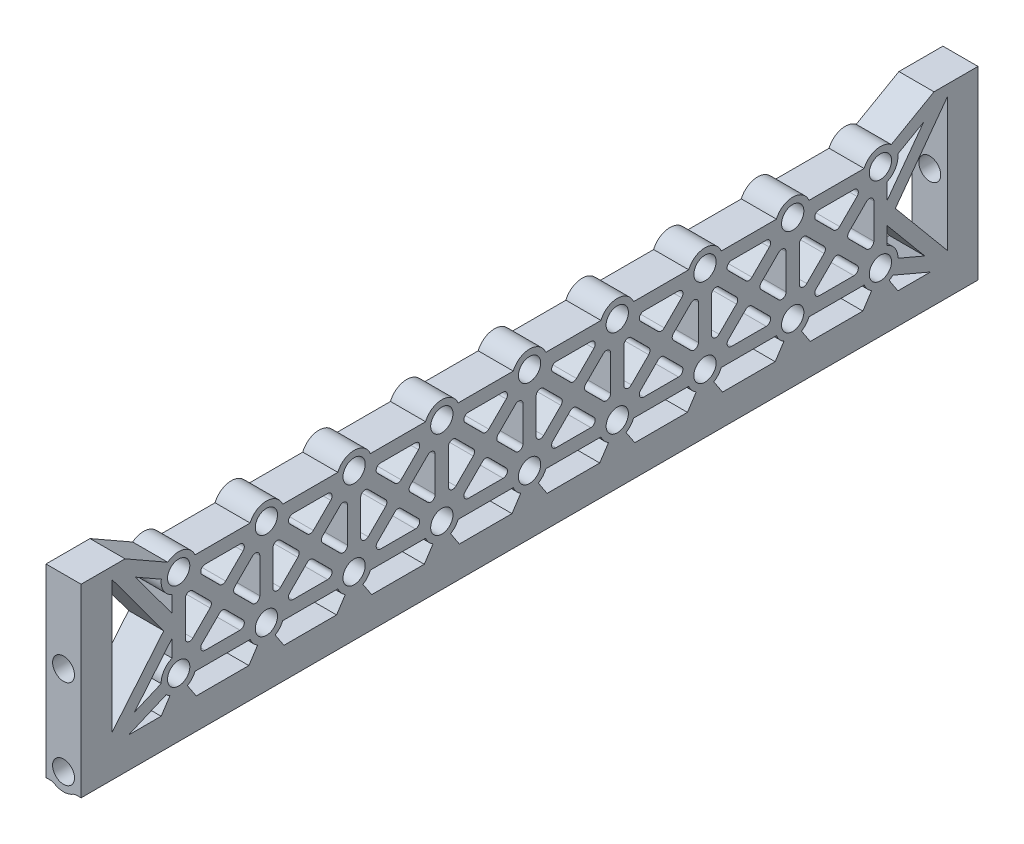
SolidWorks part; units mm, degrees
ref_plane "Front Plane" through (0, 0, 0) normal (0, 0, 1) x (1, 0, 0)
ref_plane "Top Plane" through (0, 0, 0) normal (0, 1, 0) x (1, 0, 0)
ref_plane "Right Plane" through (0, 0, 0) normal (1, 0, 0) x (0, 0, -1)
sketch "Sketch1" plane through (218.75, 0, 0) normal (1, 0, 0) x (0, 0, -1)
  line L0 (-102.25, 41.675) -> (-102.25, 55.65) construction
  line L1 (-102.25, 37.185) -> (102.25, 37.185)
  line L2 (-102.25, 37.185) -> (-102.25, -5)
  line L3 (-102.25, -5) -> (102.25, -5)
  line L4 (102.25, 37.185) -> (102.25, -5)
  line L6 (102.25, -5) -> (-102.25, -5) construction
  line L7 (102.25, 51.04) -> (102.25, 45.96) construction
extrude "Boss-Extrude1" add sketch "Sketch1" against normal blind 8
hole_wizard "Ø5.0mm Dowel Hole1" positions "Sketch4" profile "Sketch3" hole size "Ø5.0" standard "ANSI Metric"
sketch "Sketch4" plane through (0, 0, -102.25) normal (0, 0, -1) x (-1, 0, 0)
  point P0 (-214.75, 18.5)
  point P3 (-214.75, -1.825)
sketch "Sketch3" plane through (214.75, 18.5, -102.25) normal (1, 0, 0) x (0, 1, 0)
  line L0 (0, 0) -> (0, 11.5022)
  line L1 (0, 11.5022) -> (2.5, 10)
  line L2 (2.5, 10) -> (2.5, 0)
  line L5 (2.5, 0) -> (0, 0)
  line L10 (0, 11.5022) -> (-2.5, 10) construction
  line L11 (0, -6.35) -> (0, 107.95) construction
  dimension "Hole Dia." = 5
  dimension "Hole Depth" = 10
  dimension "Drill Angle" = 118
sketch "Sketch5" plane through (0, 0, -102.25) normal (0, 0, -1) x (-1, 0, 0)
  line L0 (-218.75, -5) -> (-218.75, 37.185) construction
  circle A0 centre (-214.75, -1.825) radius 4
  circle A1 centre (-214.75, -1.825) radius 2.5 construction
  circle A2 centre (-214.75, -1.825) radius 2.5
extrude "Boss-Extrude2" add sketch "Sketch5" against normal blind 10
fillet "Fillet1" radius 2 2 edges at (212.317, -5, -97.25) (217.183, -5, -97.25)
mirror "Mirror2" about plane through (0, 0, 0) normal (0, 0, 1) of "Fillet1", "Boss-Extrude2", "Ø5.0mm Dowel Hole1"
sketch "Sketch6" plane through (218.75, 0, 0) normal (1, 0, 0) x (0, 0, -1)
  line L0 (0, 28.5) -> (20, 28.5) construction
  line L1 (0, 28.5) -> (0, 8.5) construction
  line L2 (-95.25, 37.185) -> (-102.25, 37.185)
  line L3 (-102.25, 37.185) -> (-102.25, -5)
  line L4 (-102.25, -5) -> (102.25, -5)
  line L5 (102.25, -5) -> (102.25, 37.185)
  line L6 (102.25, 37.185) -> (95.25, 37.185)
  line L7 (-95.25, 37.185) -> (95.25, 37.185)
  line L10 (0, 0) -> (0, 28.5) construction
  line L11 (-95.25, 30.185) -> (-95.25, 37.185)
  line L12 (102.25, 37.185) -> (-102.25, 37.185) construction
  line L13 (95.25, 30.185) -> (95.25, 37.185)
  line L14 (95.25, 2) -> (95.25, 30.185)
  line L15 (-95.25, 2) -> (95.25, 2)
  line L16 (-95.25, 30.185) -> (-95.25, 2)
  line L17 (95.25, 30.185) -> (-95.25, 30.185)
  line L18 (95.25, 2) -> (95.25, 30.185)
  line L19 (-95.25, 2) -> (95.25, 2)
  line L20 (-95.25, 30.185) -> (-95.25, 2)
  circle A0 centre (0, 28.5) radius 2.54
  circle A1 centre (0, 28.5) radius 4
  circle A2 centre (20, 28.5) radius 4
  circle A3 centre (20, 28.5) radius 2.54
  circle A4 centre (40, 28.5) radius 4
  circle A5 centre (40, 28.5) radius 2.54
  circle A6 centre (60, 28.5) radius 4
  circle A7 centre (60, 28.5) radius 2.54
  circle A8 centre (80, 28.5) radius 4
  circle A9 centre (80, 28.5) radius 2.54
  circle A10 centre (20, 8.5) radius 4
  circle A11 centre (20, 8.5) radius 2.54
  circle A12 centre (40, 8.5) radius 4
  circle A13 centre (40, 8.5) radius 2.54
  circle A14 centre (60, 8.5) radius 4
  circle A15 centre (60, 8.5) radius 2.54
  circle A16 centre (80, 8.5) radius 4
  circle A17 centre (80, 8.5) radius 2.54
  circle A18 centre (0, 8.5) radius 4
  circle A19 centre (0, 8.5) radius 2.54
  circle A20 centre (-80, 8.5) radius 2.54
  circle A21 centre (-80, 8.5) radius 4
  circle A22 centre (-60, 8.5) radius 2.54
  circle A23 centre (-60, 8.5) radius 4
  circle A24 centre (-40, 8.5) radius 2.54
  circle A25 centre (-40, 8.5) radius 4
  circle A26 centre (-20, 8.5) radius 2.54
  circle A27 centre (-20, 8.5) radius 4
  circle A28 centre (-80, 28.5) radius 2.54
  circle A29 centre (-80, 28.5) radius 4
  circle A30 centre (-60, 28.5) radius 2.54
  circle A31 centre (-60, 28.5) radius 4
  circle A32 centre (-40, 28.5) radius 2.54
  circle A33 centre (-40, 28.5) radius 4
  circle A34 centre (-20, 28.5) radius 2.54
  circle A35 centre (-20, 28.5) radius 4
  line M6 (102.25, 37.185) -> (-102.25, 37.185)
  dimension "D3" = 5.08
  dimension "D4" = 8
  dimension "D2" = 28.5
  dimension "D7" = 20
  dimension "D8" = 20
  dimension "D1" = 7
  dimension "D5" = 5
  dimension "D6" = 2
extrude "Cut-Extrude1" cut sketch "Sketch6" against normal through all contours L11 L20 L19 L18 L13 A18 A16 A14 A12 A10 A8 A6 A4 A2 A1 A21 A23 A25 A27 A29 A31 A33 A35 M6 | A28 | A20 | A22 | A30 | A32 | A34 | A0 | A19 | A26 | A24 | A3 | A5 | A7 | A9 | A11 | A13 | A15 | A17
sketch "Sketch7" plane through (218.75, 0, 0) normal (1, 0, 0) x (0, 0, -1)
  line L0 (-80, 28.5) -> (-60, 28.5) construction
  line L1 (-60, 28.5) -> (-60, 8.5) construction
  line L2 (-60, 8.5) -> (-80, 8.5) construction
  line L3 (-80, 8.5) -> (-80, 28.5) construction
  line L4 (-80, 28.5) -> (-60, 8.5) construction
  line L5 (-80, 8.5) -> (-60, 28.5) construction
  line L6 (-74.6716, 25.2929) -> (-70.7071, 21.3284)
  line L7 (-76.2919, 30) -> (-63.7081, 30)
  line L8 (-58.5, 24.7919) -> (-58.5, 12.2081)
  line L9 (-78.9393, 29.5607) -> (-58.9393, 9.5607) construction
  line L10 (-73.9645, 27) -> (-66.0355, 27)
  line L11 (-63.7081, 7) -> (-76.2919, 7)
  line L12 (-69.2929, 21.3284) -> (-65.3284, 25.2929)
  line L13 (-81.5, 12.2081) -> (-81.5, 24.7919)
  line L14 (-58.5, 7) -> (-81.5, 7) construction
  line L15 (-58.5, 30) -> (-58.5, 7) construction
  line L16 (-81.5, 30) -> (-58.5, 30) construction
  line L17 (-81.5, 7) -> (-81.5, 30) construction
  line L18 (-61.5, 22.4645) -> (-61.5, 14.5355)
  line L19 (-67.1716, 17.7929) -> (-63.2071, 13.8284)
  line L20 (-63.2071, 23.1716) -> (-67.1716, 19.2071)
  line L21 (-66.0355, 10) -> (-73.9645, 10)
  line L22 (-70.7071, 15.6716) -> (-74.6716, 11.7071)
  line L23 (-65.3284, 11.7071) -> (-69.2929, 15.6716)
  line L24 (-78.5, 14.5355) -> (-78.5, 22.4645)
  line L25 (-72.8284, 19.2071) -> (-76.7929, 23.1716)
  line L26 (-76.7929, 13.8284) -> (-72.8284, 17.7929)
  line L27 (-70, 18.5) -> (-69.2929, 21.3284) construction
  arc A0 (-70.7071, 21.3284) -> (-69.2929, 21.3284) centre (-70, 22.0355) ccw
  arc A1 (-65.3284, 25.2929) -> (-66.0355, 27) centre (-66.0355, 26) ccw
  arc A2 (-73.9645, 27) -> (-74.6716, 25.2929) centre (-73.9645, 26) ccw
  circle A3 centre (-80, 8.5) radius 4 construction
  circle A4 centre (-60, 8.5) radius 4 construction
  circle A5 centre (-60, 28.5) radius 4 construction
  circle A6 centre (-80, 28.5) radius 4 construction
  arc A7 (-76.2919, 7) -> (-81.5, 12.2081) centre (-80, 8.5) ccw
  arc A8 (-58.5, 12.2081) -> (-63.7081, 7) centre (-60, 8.5) ccw
  arc A9 (-63.7081, 30) -> (-58.5, 24.7919) centre (-60, 28.5) ccw
  arc A10 (-81.5, 24.7919) -> (-76.2919, 30) centre (-80, 28.5) ccw
  arc A11 (-61.5, 22.4645) -> (-63.2071, 23.1716) centre (-62.5, 22.4645) ccw
  arc A12 (-63.2071, 13.8284) -> (-61.5, 14.5355) centre (-62.5, 14.5355) ccw
  arc A13 (-67.1716, 19.2071) -> (-67.1716, 17.7929) centre (-66.4645, 18.5) ccw
  arc A14 (-66.0355, 10) -> (-65.3284, 11.7071) centre (-66.0355, 11) ccw
  arc A15 (-74.6716, 11.7071) -> (-73.9645, 10) centre (-73.9645, 11) ccw
  arc A16 (-69.2929, 15.6716) -> (-70.7071, 15.6716) centre (-70, 14.9645) ccw
  arc A17 (-78.5, 14.5355) -> (-76.7929, 13.8284) centre (-77.5, 14.5355) ccw
  arc A18 (-76.7929, 23.1716) -> (-78.5, 22.4645) centre (-77.5, 22.4645) ccw
  arc A19 (-72.8284, 17.7929) -> (-72.8284, 19.2071) centre (-73.5355, 18.5) ccw
  point P2 (-70, 18.5)
  dimension "D4" = 1
  dimension "D2" = 1.5
  dimension "D3" = 1.5
  dimension "D7" = 2.9155
  dimension "D1" = 1.5
  dimension "D5" = 1.5
  dimension "D6" = 4
extrude "Boss-Extrude3" add sketch "Sketch7" against normal up to surface (8 mm away) up to face at (210.75, 28.5, 57.46)
pattern_linear "LPattern1" count 8 spacing 20 along (0, 0, -1) of "Boss-Extrude3"
sketch "Sketch8" plane through (218.75, 0, 0) normal (1, 0, 0) x (0, 0, -1)
  line L0 (-95.25, 37.185) -> (-80, 28.5) construction
  line L2 (-81.5, 24.7919) -> (-81.5, 12.2081) construction
  line L3 (-80, 8.5) -> (-95.25, 2) construction
  line L5 (-95.25, 37.185) -> (-81.5, 18.5) construction
  line L6 (-81.5, 18.5) -> (-95.25, 2) construction
  line L7 (-95.25, 34.6542) -> (-82.489, 17.3132)
  line L8 (-92.219, 37.185) -> (-82.4799, 31.6385)
  line L10 (-81.5, 16.1569) -> (-90.1146, 5.8194)
  line L11 (-83.9993, 8.4259) -> (-90.1146, 5.8194)
  line L12 (-89.8573, 32.3876) -> (-81.5, 21.0308)
  line L13 (-89.8573, 32.3876) -> (-83.9645, 29.0316)
  line L16 (-82.823, 5.6662) -> (-91.4244, 2)
  line L17 (-81.5, 24.7919) -> (-81.5, 12.2081)
  line L18 (-95.25, 37.185) -> (-95.25, 2)
  line L19 (-95.25, 2) -> (-91.4244, 2)
  line L20 (-95.25, 2) -> (95.25, 2) construction
  line L21 (-95.25, 37.185) -> (-92.219, 37.185)
  line L22 (-100.6427, 41.9824) -> (-79.2577, 29.8034) construction
  line L23 (-100.6427, 41.9824) -> (-82.7081, 17.611) construction
  line L24 (-82.6523, 19.4603) -> (-100.3854, -1.8194) construction
  line L25 (-79.4119, 7.1201) -> (-100.3854, -1.8194) construction
  line L26 (-89.8573, 32.3876) -> (-80.7423, 27.1966) construction
  line L27 (-80.5881, 9.8799) -> (-90.1146, 5.8194) construction
  line L28 (-80.3477, 17.5397) -> (-90.1146, 5.8194) construction
  line L29 (-89.8573, 32.3876) -> (-80.2919, 19.389) construction
  line L31 (-82.4157, 19.7443) -> (-95.25, 4.3431)
  arc A1 (-81.5, 12.2081) -> (-76.2919, 7) centre (-80, 8.5) ccw construction
  arc A2 (-76.2919, 30) -> (-81.5, 24.7919) centre (-80, 28.5) ccw construction
  arc A3 (-81.5, 12.2081) -> (-76.2919, 7) centre (-80, 8.5) ccw
  arc A4 (-76.2919, 30) -> (-81.5, 24.7919) centre (-80, 28.5) ccw
  dimension "D1" = 1.5
  dimension "D3" = 1.5
  dimension "D2" = 1.5
extrude "Boss-Extrude4" add sketch "Sketch8" against normal up to surface (8 mm away) up to face at (210.75, 17.8425, 0)
mirror "Mirror3" about plane through (0, 0, 0) normal (0, 0, 1) of "Boss-Extrude4"
sketch "Sketch9" plane through (218.75, 0, 0) normal (1, 0, 0) x (0, 0, -1)
  line L0 (-82, 5.0359) -> (-78, 5.0359) construction
  line L1 (-78, 5.0359) -> (-76, 2)
  line L2 (-91.4244, 2) -> (91.4244, 2) construction
  line L3 (-76, 2) -> (-84, 2)
  line L4 (-84, 2) -> (-82, 5.0359)
  line L5 (-82, 5.0359) -> (-78, 5.0359)
  arc A0 (-82.823, 5.6662) -> (-76.2919, 7) centre (-80, 8.5) ccw construction
  dimension "D1" = 4
  dimension "D2" = 8
extrude "Boss-Extrude5" add sketch "Sketch9" against normal up to surface (8 mm away) contours L5 L4 L3 L1 up to face at (210.75, 29.2755, 0)
pattern_linear "LPattern2" count 9 spacing 20 along (0, 0, -1) of "Boss-Extrude5"
